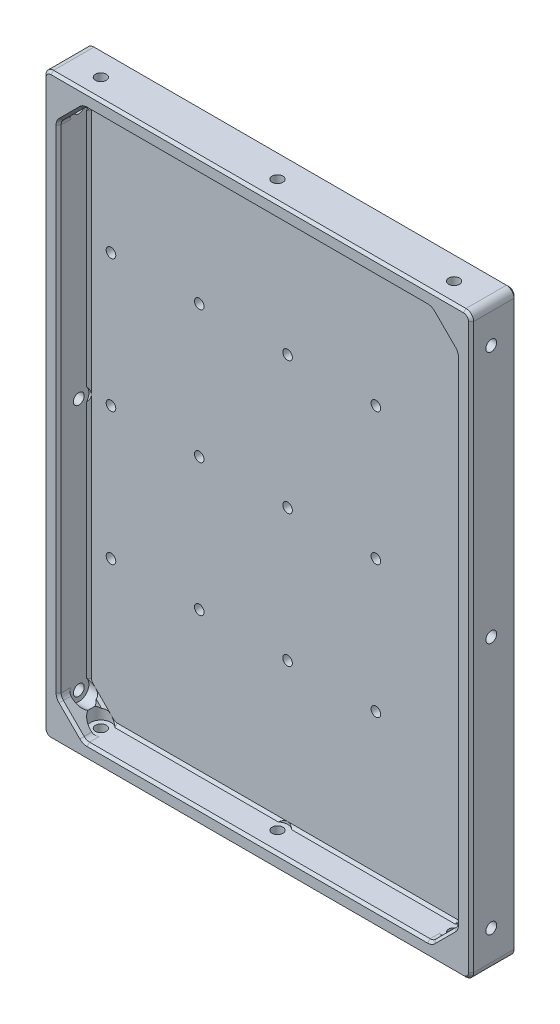
SolidWorks part; units mm, degrees
ref_plane "正面" through (0, 0, 0) normal (0, 0, 1) x (1, 0, 0)
ref_plane "平面" through (0, 0, 0) normal (0, 1, 0) x (1, 0, 0)
ref_plane "右側面" through (0, 0, 0) normal (1, 0, 0) x (0, 0, -1)
sketch "ｽｹｯﾁ1" plane through (0, 0, 0) normal (0, 0, 1) x (1, 0, 0)
  line L1 (84.75, -114.75) -> (-84.75, -114.75)
  line L2 (84.75, -114.75) -> (84.75, 114.75)
  line L3 (84.75, 114.75) -> (-84.75, 114.75)
  line L4 (-84.75, -114.75) -> (-84.75, 114.75)
  line L5 (84.75, -114.75) -> (-84.75, 114.75) construction
  line L6 (84.75, 114.75) -> (-84.75, -114.75) construction
  point P0 (0, 0)
  dimension "D1" = 229.5
  dimension "D2" = 169.5
extrude "ﾎﾞｽ - 押し出し1" add sketch "ｽｹｯﾁ1" along normal blind 6
sketch "ｽｹｯﾁ2" plane through (0, 0, 6) normal (0, 0, 1) x (1, 0, 0)
  line L1 (78.75, -108.75) -> (-78.75, -108.75)
  line L2 (78.75, -108.75) -> (78.75, 108.75)
  line L3 (78.75, 108.75) -> (-78.75, 108.75)
  line L4 (-84.75, 114.75) -> (-84.75, -114.75)
  line L5 (-84.75, -114.75) -> (84.75, -114.75)
  line L6 (84.75, -114.75) -> (84.75, 114.75)
  line L7 (84.75, 114.75) -> (-84.75, 114.75)
  line L8 (-84.75, 114.75) -> (-84.75, -114.75)
  line L9 (-84.75, -114.75) -> (84.75, -114.75)
  line L10 (84.75, -114.75) -> (84.75, 114.75)
  line L11 (84.75, 114.75) -> (-84.75, 114.75)
  line L12 (-78.75, -108.75) -> (-78.75, 108.75)
  line L13 (78.75, -108.75) -> (-78.75, 108.75) construction
  line L14 (78.75, 108.75) -> (-78.75, -108.75) construction
  point P2 (0, 0)
  dimension "D2" = 6
  dimension "D3" = 6
  dimension "D1" = 0
extrude "ﾎﾞｽ - 押し出し2" add sketch "ｽｹｯﾁ2" along normal blind 12
chamfer "面取り1" distance 10 angle 45 4 edges at (-78.75, -108.75, 12) (78.75, -108.75, 12) (78.75, 108.75, 12) (-78.75, 108.75, 12)
fillet "ﾌｨﾚｯﾄ1" radius 3 8 edges at (68.75, 108.75, 12) (78.75, 98.75, 12) (-68.75, 108.75, 12) (-78.75, 98.75, 12) (-78.75, -98.75, 12) (-68.75, -108.75, 12) (68.75, -108.75, 12) (78.75, -98.75, 12)
chamfer "面取り2" distance 1 angle 45 32 edges at (78.75, 0, 18) (78.5216, 98.6554, 18) (78.5216, -98.6554, 18) (73.75, 103.75, 18) (73.75, -103.75, 18) (68.6554, 108.5216, 18) (68.6554, -108.5216, 18) (0, 108.75, 18) (0, -108.75, 18) (-68.6554, 108.5216, 18) (-68.6554, -108.5216, 18) (-73.75, 103.75, 18) (-73.75, -103.75, 18) (-78.5216, 98.6554, 18) (-78.5216, -98.6554, 18) (-78.75, 0, 18) (78.75, 0, 6) (78.5216, 98.6554, 6) (78.5216, -98.6554, 6) (73.75, 103.75, 6) (73.75, -103.75, 6) (68.6554, 108.5216, 6) (68.6554, -108.5216, 6) (0, 108.75, 6) (0, -108.75, 6) (-68.6554, 108.5216, 6) (-68.6554, -108.5216, 6) (-73.75, 103.75, 6) (-73.75, -103.75, 6) (-78.5216, 98.6554, 6) (-78.5216, -98.6554, 6) (-78.75, 0, 6)
fillet "ﾌｨﾚｯﾄ2" radius 3 4 edges at (84.75, 114.75, 9) (-84.75, 114.75, 9) (84.75, -114.75, 9) (-84.75, -114.75, 9)
chamfer "面取り3" distance 1 angle 45 16 edges at (-84.75, 0, 18) (-83.8713, -113.8713, 18) (-83.8713, 113.8713, 18) (0, -114.75, 18) (0, 114.75, 18) (83.8713, -113.8713, 18) (83.8713, 113.8713, 18) (84.75, 0, 18) (-84.75, 0, 0) (-83.8713, -113.8713, 0) (-83.8713, 113.8713, 0) (0, -114.75, 0) (0, 114.75, 0) (83.8713, -113.8713, 0) (83.8713, 113.8713, 0) (84.75, 0, 0)
ref_plane "平面1" through (-68.75, 0, 0) normal (1, 0, 0) x (0, 0, -1)
sketch "ｽｹｯﾁ4" plane through (-68.75, 0, 0) normal (1, 0, 0) x (0, 0, -1)
  line L0 (-10, 100) -> (-10, -100)
  dimension "D1" = 10
  dimension "D2" = 200
  dimension "D3" = 100
hole_wizard "M4 六角穴付き頭ねじ用座ぐり穴1" positions "ｽｹｯﾁ5" profile "ｽｹｯﾁ7" counterbore size "M4" standard "ISO"
sketch "ｽｹｯﾁ5" plane through (-68.75, 0, 0) normal (1, 0, 0) x (0, 0, -1)
  line L0 (-10, 100) -> (-10, -100) construction
  point P0 (-10, 0)
  point P4 (-10, 100)
  point P7 (-10, -100)
sketch "ｽｹｯﾁ7" plane through (-68.75, 0, 10) normal (0, 1, 0) x (0, 0, -1)
  line L0 (0, 0) -> (0, 16)
  line L1 (0, 16) -> (2.15, 16)
  line L3 (2.15, 16) -> (2.15, 10)
  line L4 (2.15, 10) -> (4, 10)
  line L5 (4, 10) -> (4, 0)
  line L7 (4, 0) -> (0, 0)
  line L11 (0, -6.35) -> (0, 107.95) construction
  dimension "通し穴の直径" = 4.3
  dimension "通し穴の深さ" = 16
  dimension "座ぐり穴の直径" = 8
  dimension "座ぐり穴の深さ" = 10
mirror "ﾐﾗｰ1" about plane through (0, 0, 0) normal (1, 0, 0) of "M4 六角穴付き頭ねじ用座ぐり穴1"
ref_plane "平面2" through (0, 98.75, 0) normal (0, -1, 0) x (-1, 0, 0)
sketch "ｽｹｯﾁ8" plane through (0, 98.75, 0) normal (0, -1, 0) x (-1, 0, 0)
  line L0 (-70, -10) -> (70, -10)
  line L1 (-81.75, 0) -> (81.75, 0) construction
  dimension "D1" = 10
  dimension "D2" = 140
  dimension "D3" = 70
hole_wizard "M4 六角穴付き頭ねじ用座ぐり穴2" positions "ｽｹｯﾁ9" profile "ｽｹｯﾁ10" counterbore size "M4" standard "ISO"
sketch "ｽｹｯﾁ9" plane through (0, 98.75, 0) normal (0, -1, 0) x (-1, 0, 0)
  point P0 (-70, -10)
  point P3 (70, -10)
  point P6 (0, -10)
sketch "ｽｹｯﾁ10" plane through (70, 98.75, 10) normal (1, 0, 0) x (0, 0, -1)
  line L0 (0, 0) -> (0, 16)
  line L1 (0, 16) -> (2.15, 16)
  line L3 (2.15, 16) -> (2.15, 10)
  line L4 (2.15, 10) -> (4, 10)
  line L5 (4, 10) -> (4, 0)
  line L7 (4, 0) -> (0, 0)
  line L11 (0, -6.35) -> (0, 107.95) construction
  dimension "通し穴の直径" = 4.3
  dimension "通し穴の深さ" = 16
  dimension "座ぐり穴の直径" = 8
  dimension "座ぐり穴の深さ" = 10
mirror "ﾐﾗｰ2" about plane through (0, 0, 0) normal (0, 1, 0) of "M4 六角穴付き頭ねじ用座ぐり穴2"
sketch "ｽｹｯﾁ11" plane through (0, 0, 6) normal (0, 0, 1) x (1, 0, 0)
  line L1 (25, -68) -> (-25, -68)
  line L2 (25, -68) -> (25, 82)
  line L3 (25, 82) -> (-25, 82)
  line L4 (-25, -68) -> (-25, 82)
  line L5 (25, -68) -> (-25, 82) construction
  line L6 (25, 82) -> (-25, -68) construction
  point P0 (0, 0)
  point P9 (0, 7)
  dimension "D1" = 150
  dimension "D2" = 50
  dimension "D3" = 7
sketch "ｽｹｯﾁ12" plane through (0, 0, 0) normal (0, 0, -1) x (-1, 0, 0)
  line L1 (70, -52.5) -> (-70, -52.5)
  line L2 (70, -52.5) -> (70, 52.5)
  line L3 (70, 52.5) -> (-70, 52.5)
  line L4 (-70, -52.5) -> (-70, 52.5)
  line L5 (70, -52.5) -> (-70, 52.5) construction
  line L6 (70, 52.5) -> (-70, -52.5) construction
  line L7 (0, 52.5) -> (0, -52.5)
  line L8 (35, -52.5) -> (-35, -52.5)
  line L9 (35, -52.5) -> (35, 52.5)
  line L10 (35, 52.5) -> (-35, 52.5)
  line L11 (-35, -52.5) -> (-35, 52.5)
  line L12 (35, -52.5) -> (-35, 52.5) construction
  line L13 (35, 52.5) -> (-35, -52.5) construction
  point P0 (0, 0)
  point P8 (0, 0)
  dimension "D1" = 105
  dimension "D2" = 140
  dimension "D3" = 35
hole_wizard "M4 すきま穴1" positions "ｽｹｯﾁ13" profile "ｽｹｯﾁ14" hole size "M4" standard "ISO" end condition through all
sketch "ｽｹｯﾁ13" plane through (0, 0, 0) normal (0, 0, -1) x (-1, 0, 0)
  line L0 (-70, -52.5) -> (-70, 52.5) construction
  line L1 (-35, -52.5) -> (-35, 52.5) construction
  line L2 (35, -52.5) -> (35, 52.5) construction
  line L3 (70, -52.5) -> (70, 52.5) construction
  point P0 (-70, 52.5)
  point P3 (-70, -52.5)
  point P6 (-35, -52.5)
  point P9 (-35, 52.5)
  point P12 (0, 52.5)
  point P15 (0, -52.5)
  point P18 (35, -52.5)
  point P21 (70, -52.5)
  point P24 (70, 52.5)
  point P27 (35, 52.5)
  point P30 (-70, 0)
  point P34 (-35, 0)
  point P38 (0, 0)
  point P41 (35, 0)
  point P45 (70, 0)
sketch "ｽｹｯﾁ14" plane through (70, 52.5, 0) normal (1, 0, 0) x (0, 1, 0)
  line L0 (0, 0) -> (0, 18)
  line L1 (0, 18) -> (1.9, 18)
  line L2 (1.9, 18) -> (1.9, 0)
  line L5 (1.9, 0) -> (0, 0)
  line L11 (0, -6.35) -> (0, 107.95) construction
  dimension "通し穴の直径" = 3.8
  dimension "通し穴の深さ" = 18
